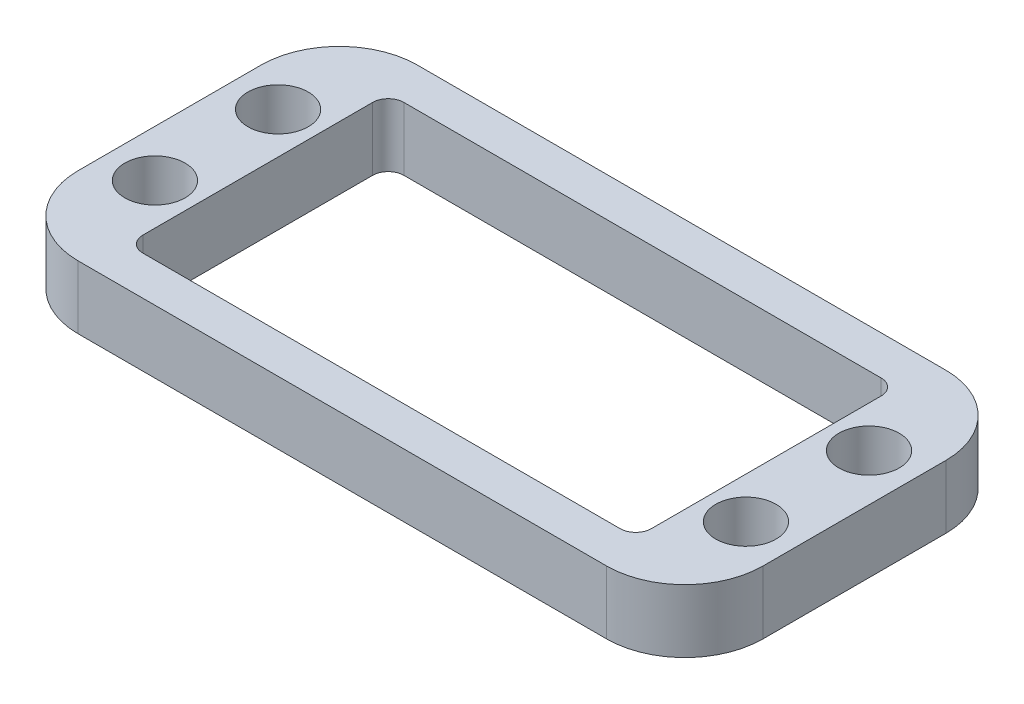
SolidWorks part; units mm, degrees
material "ABS"
ref_plane "Front Plane" through (0, 0, 0) normal (0, 0, 1) x (1, 0, 0)
ref_plane "Top Plane" through (0, 0, 0) normal (0, 1, 0) x (1, 0, 0)
ref_plane "Right Plane" through (0, 0, 0) normal (1, 0, 0) x (0, 0, -1)
sketch "Sketch1" plane through (0, 0, 0) normal (0, 1, 0) x (1, 0, 0)
  line L1 (-20.65, 10.6) -> (20.65, 10.6)
  line L2 (-20.65, 10.6) -> (-20.65, -10.6)
  line L3 (-20.65, -10.6) -> (20.65, -10.6)
  line L4 (20.65, 10.6) -> (20.65, -10.6)
  line L5 (-20.65, 10.6) -> (20.65, -10.6) construction
  line L6 (-20.65, -10.6) -> (20.65, 10.6) construction
  line L7 (-27.81, 13.775) -> (27.81, 13.775)
  line L8 (-27.81, 13.775) -> (-27.81, -13.775)
  line L9 (-27.81, -13.775) -> (27.81, -13.775)
  line L10 (27.81, 13.775) -> (27.81, -13.775)
  line L11 (-27.81, 13.775) -> (27.81, -13.775) construction
  line L12 (-27.81, -13.775) -> (27.81, 13.775) construction
  point P0 (0, 0)
  point P6 (0, 0)
  dimension "D1" = 41.3
  dimension "D2" = 21.2
  dimension "D3" = 3.175
  dimension "D4" = 55.62
extrude "Boss-Extrude1" add sketch "Sketch1" along normal blind 5.1308
hole_wizard "Ø4.9 (4.9) Diameter Hole1" positions "Sketch2" profile "Sketch3" hole size "Ø4.9" standard "ANSI Metric" end condition through all
sketch "Sketch2" plane through (0, 5.1308, 0) normal (0, 1, 0) x (1, 0, 0)
  line L1 (-24, 5) -> (24, 5)
  line L2 (-24, 5) -> (-24, -5)
  line L3 (-24, -5) -> (24, -5)
  line L4 (24, 5) -> (24, -5)
  line L5 (-24, 5) -> (24, -5) construction
  line L6 (-24, -5) -> (24, 5) construction
  point P2 (24, -5)
  point P151 (-24, 5)
  point P152 (-24, -5)
  point P153 (24, 5)
  point P159 (0, 0)
  dimension "D1" = 48
  dimension "D2" = 10
sketch "Sketch3" plane through (24, 5.1308, 5) normal (1, 0, 0) x (0, 0, 1)
  line L0 (0, 0) -> (0, 5.1308)
  line L1 (0, 5.1308) -> (2.45, 5.1308)
  line L2 (2.45, 5.1308) -> (2.45, 0)
  line L5 (2.45, 0) -> (0, 0)
  line L11 (0, -6.35) -> (0, 107.95) construction
  dimension "Thru Hole Dia." = 4.9
  dimension "Thru Hole Depth" = 5.1308
fillet "Fillet1" radius 6.35 4 edges at (27.81, 2.5654, 13.775) (27.81, 2.5654, -13.775) (-27.81, 2.5654, 13.775) (-27.81, 2.5654, -13.775)
fillet "Fillet2" radius 1.27 4 edges at (-20.65, 2.5654, 10.6) (20.65, 2.5654, 10.6) (20.65, 2.5654, -10.6) (-20.65, 2.5654, -10.6)
equation "\"D1@Sketch1\" = 40.3mm + 2 * \"gap\""
equation "\"D2@Sketch1\"= 20.2mm + 2 * \"gap\""
equation "\"D3@Sketch1\"=0.125"
equation "\"D4@Sketch1\"= 48mm + 0.3in"
equation "\"gap\"= 0.5mm"
